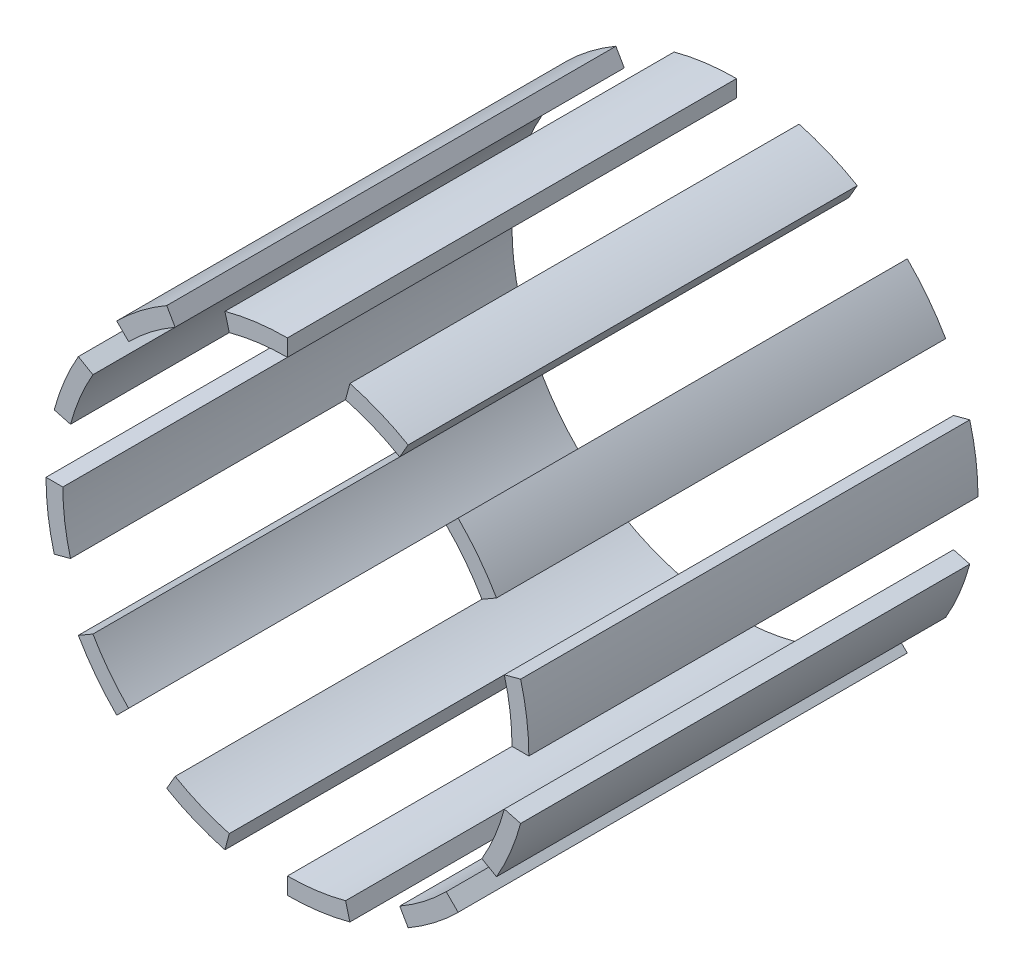
SolidWorks part; units mm, degrees
material "3.0255 (EN-AW 1350A)"
ref_plane "Plan de face" through (0, 0, 0) normal (0, 0, 1) x (1, 0, 0)
ref_plane "Plan de dessus" through (0, 0, 0) normal (0, 1, 0) x (1, 0, 0)
ref_plane "Plan de droite" through (0, 0, 0) normal (1, 0, 0) x (0, 0, -1)
sketch "Esquisse1" plane through (0, 0, 0) normal (0, 0, 1) x (1, 0, 0)
  line L0 (0, 0) -> (8.6, 0) construction
  line L1 (8, 0) -> (8.6, 0)
  line L2 (7.7274, 2.0706) -> (8.307, 2.2258)
  line L3 (7.7274, -2.0706) -> (8.307, -2.2258)
  line L4 (6.9282, -4) -> (7.4478, -4.3)
  line L5 (5.6569, -5.6569) -> (6.0811, -6.0811)
  line L6 (4, -6.9282) -> (4.3, -7.4478)
  line L7 (2.0706, -7.7274) -> (2.2258, -8.307)
  line L8 (0, -8) -> (0, -8.6)
  line L9 (-2.0706, -7.7274) -> (-2.2258, -8.307)
  line L10 (-4, -6.9282) -> (-4.3, -7.4478)
  line L11 (-5.6569, -5.6569) -> (-6.0811, -6.0811)
  line L12 (-6.9282, -4) -> (-7.4478, -4.3)
  line L13 (-7.7274, -2.0706) -> (-8.307, -2.2258)
  line L14 (-8, 0) -> (-8.6, 0)
  line L15 (-7.7274, 2.0706) -> (-8.307, 2.2258)
  line L16 (-6.9282, 4) -> (-7.4478, 4.3)
  line L17 (-5.6569, 5.6569) -> (-6.0811, 6.0811)
  line L18 (-4, 6.9282) -> (-4.3, 7.4478)
  line L19 (-2.0706, 7.7274) -> (-2.2258, 8.307)
  line L20 (0, 8) -> (0, 8.6)
  line L21 (2.0706, 7.7274) -> (2.2258, 8.307)
  line L22 (4, 6.9282) -> (4.3, 7.4478)
  line L23 (5.6569, 5.6569) -> (6.0811, 6.0811)
  line L24 (6.9282, 4) -> (7.4478, 4.3)
  arc A0 (8, 0) -> (7.7274, 2.0706) centre (0, 0) ccw
  arc A1 (8.6, 0) -> (8.307, 2.2258) centre (0, 0) ccw
  arc A2 (6.9282, -4) -> (7.7274, -2.0706) centre (0, 0) ccw
  arc A3 (7.4478, -4.3) -> (8.307, -2.2258) centre (0, 0) ccw
  arc A4 (4, -6.9282) -> (5.6569, -5.6569) centre (0, 0) ccw
  arc A5 (4.3, -7.4478) -> (6.0811, -6.0811) centre (0, 0) ccw
  arc A6 (0, -8) -> (2.0706, -7.7274) centre (0, 0) ccw
  arc A7 (0, -8.6) -> (2.2258, -8.307) centre (0, 0) ccw
  arc A8 (-4, -6.9282) -> (-2.0706, -7.7274) centre (0, 0) ccw
  arc A9 (-4.3, -7.4478) -> (-2.2258, -8.307) centre (0, 0) ccw
  arc A10 (-6.9282, -4) -> (-5.6569, -5.6569) centre (0, 0) ccw
  arc A11 (-7.4478, -4.3) -> (-6.0811, -6.0811) centre (0, 0) ccw
  arc A12 (-8, 0) -> (-7.7274, -2.0706) centre (0, 0) ccw
  arc A13 (-8.6, 0) -> (-8.307, -2.2258) centre (0, 0) ccw
  arc A14 (-6.9282, 4) -> (-7.7274, 2.0706) centre (0, 0) ccw
  arc A15 (-7.4478, 4.3) -> (-8.307, 2.2258) centre (0, 0) ccw
  arc A16 (-4, 6.9282) -> (-5.6569, 5.6569) centre (0, 0) ccw
  arc A17 (-4.3, 7.4478) -> (-6.0811, 6.0811) centre (0, 0) ccw
  arc A18 (0, 8) -> (-2.0706, 7.7274) centre (0, 0) ccw
  arc A19 (0, 8.6) -> (-2.2258, 8.307) centre (0, 0) ccw
  arc A20 (4, 6.9282) -> (2.0706, 7.7274) centre (0, 0) ccw
  arc A21 (4.3, 7.4478) -> (2.2258, 8.307) centre (0, 0) ccw
  arc A22 (6.9282, 4) -> (5.6569, 5.6569) centre (0, 0) ccw
  arc A23 (7.4478, 4.3) -> (6.0811, 6.0811) centre (0, 0) ccw
  point P53 (0, 0)
  dimension "D1" = 16
  dimension "D2" = 0.6
  dimension "D3" = 15
  dimension "D4" = 0.6
  dimension "D5" = 12
extrude "Boss.-Extru.1" add sketch "Esquisse1" along normal blind 16
